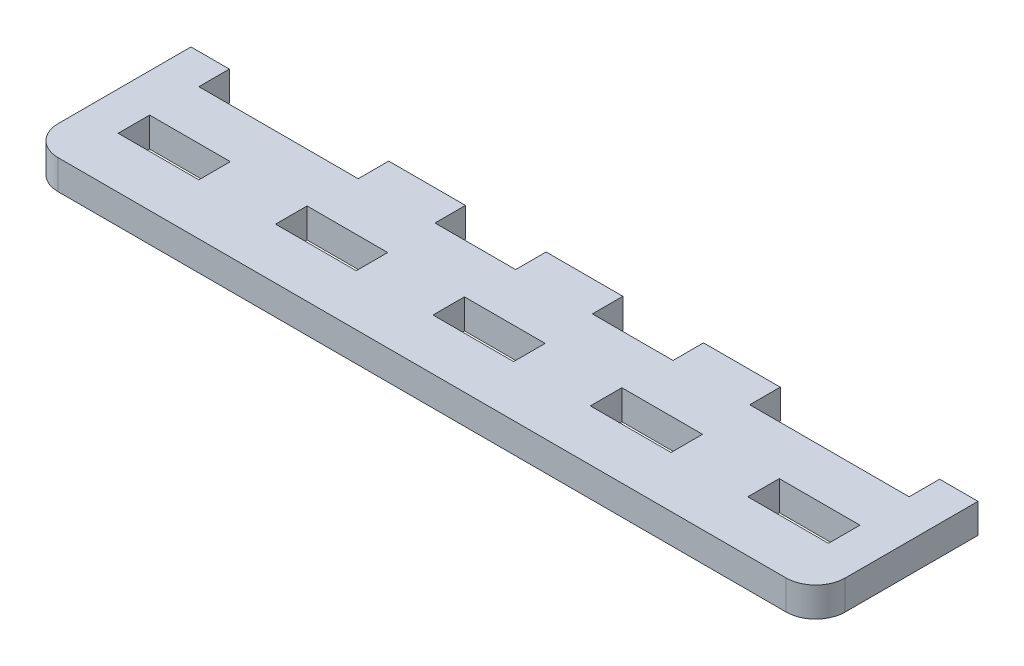
SolidWorks part; units mm, degrees
ref_plane "Front Plane" through (0, 0, 0) normal (0, 0, 1) x (1, 0, 0)
ref_plane "Top Plane" through (0, 0, 0) normal (0, 1, 0) x (1, 0, 0)
ref_plane "Right Plane" through (0, 0, 0) normal (1, 0, 0) x (0, 0, -1)
sketch "Sketch1" plane through (0, 0, 0) normal (0, 1, 0) x (1, 0, 0)
  line L0 (80, -80) -> (80, 0) construction
  line L1 (0, 0) -> (80, 0)
  line L2 (0, 0) -> (0, -16.5)
  line L3 (0, -16.5) -> (80, -16.5)
  line L4 (80, 0) -> (80, -16.5)
sketch "Sketch2" plane through (0, 0, 0) normal (1, 0, 0) x (0, 0, -1)
  line L1 (0, 0) -> (-16.5, 0)
  line L2 (0, 0) -> (0, -3)
  line L3 (0, -3) -> (-16.5, -3)
  line L4 (-16.5, 0) -> (-16.5, -3)
extrude "Boss-Extrude1" add sketch "Sketch1" against normal up to vertex (3 mm away) up to point (0, -3, 0)
sketch "Sketch3" plane through (0, 0, 0) normal (0, 1, 0) x (1, 0, 0)
  line L4 (12, -11.2) -> (12, -8.2)
  line L5 (12, -8.2) -> (4, -8.2)
  line L6 (4, -8.2) -> (4, -11.2)
  line L7 (4, -11.2) -> (12, -11.2)
  line L8 (12, -11.2) -> (12, -8.2) construction
  line L9 (12, -8.2) -> (4, -8.2) construction
  line L10 (4, -8.2) -> (4, -11.2) construction
  line L11 (4, -11.2) -> (12, -11.2) construction
  line L12 (28, 0) -> (28, -3)
  line L13 (36, 0) -> (28, 0)
  line L14 (36, -3) -> (36, 0)
  line L15 (28, -3) -> (36, -3)
  line L16 (28, 0) -> (28, -3) construction
  line L17 (36, 0) -> (28, 0) construction
  line L18 (36, -3) -> (36, 0) construction
  line L19 (28, -3) -> (36, -3) construction
  line L20 (36, -8.2) -> (36, -11.2)
  line L21 (44, -8.2) -> (36, -8.2)
  line L22 (44, -11.2) -> (44, -8.2)
  line L23 (36, -11.2) -> (44, -11.2)
  line L24 (36, -8.2) -> (36, -11.2) construction
  line L25 (44, -8.2) -> (36, -8.2) construction
  line L26 (44, -11.2) -> (44, -8.2) construction
  line L27 (36, -11.2) -> (44, -11.2) construction
  line L28 (20, -8.2) -> (20, -11.2)
  line L29 (28, -8.2) -> (20, -8.2)
  line L30 (28, -11.2) -> (28, -8.2)
  line L31 (20, -11.2) -> (28, -11.2)
  line L32 (20, -8.2) -> (20, -11.2) construction
  line L33 (28, -8.2) -> (20, -8.2) construction
  line L34 (28, -11.2) -> (28, -8.2) construction
  line L35 (20, -11.2) -> (28, -11.2) construction
  line L36 (20, -3) -> (20, 0)
  line L37 (20, 0) -> (4, 0)
  line L38 (4, 0) -> (4, -3)
  line L39 (4, -3) -> (20, -3)
  line L40 (20, -3) -> (20, 0) construction
  line L41 (20, 0) -> (4, 0) construction
  line L42 (4, 0) -> (4, -3) construction
  line L43 (4, -3) -> (20, -3) construction
  line L44 (44, 0) -> (44, -3)
  line L45 (52, 0) -> (44, 0)
  line L46 (52, -3) -> (52, 0)
  line L47 (44, -3) -> (52, -3)
  line L48 (44, 0) -> (44, -3) construction
  line L49 (52, 0) -> (44, 0) construction
  line L50 (52, -3) -> (52, 0) construction
  line L51 (44, -3) -> (52, -3) construction
  line L52 (60, -11.2) -> (60, -8.2)
  line L53 (60, -8.2) -> (52, -8.2)
  line L54 (52, -8.2) -> (52, -11.2)
  line L55 (52, -11.2) -> (60, -11.2)
  line L56 (60, -11.2) -> (60, -8.2) construction
  line L57 (60, -8.2) -> (52, -8.2) construction
  line L58 (52, -8.2) -> (52, -11.2) construction
  line L59 (52, -11.2) -> (60, -11.2) construction
  line L60 (68, -8.2) -> (68, -11.2)
  line L61 (76, -8.2) -> (68, -8.2)
  line L62 (76, -11.2) -> (76, -8.2)
  line L63 (68, -11.2) -> (76, -11.2)
  line L64 (68, -8.2) -> (68, -11.2) construction
  line L65 (76, -8.2) -> (68, -8.2) construction
  line L66 (76, -11.2) -> (76, -8.2) construction
  line L67 (68, -11.2) -> (76, -11.2) construction
  line L68 (76, 0) -> (60, 0)
  line L69 (60, 0) -> (60, -3)
  line L70 (60, -3) -> (76, -3)
  line L71 (76, -3) -> (76, 0)
  line L72 (76, 0) -> (60, 0) construction
  line L73 (60, 0) -> (60, -3) construction
  line L74 (60, -3) -> (76, -3) construction
  line L75 (76, -3) -> (76, 0) construction
  line L108 (12.1, -11.3) -> (12.1, -8.1)
  line L109 (12.1, -8.1) -> (3.9, -8.1)
  line L110 (3.9, -8.1) -> (3.9, -11.3)
  line L111 (3.9, -11.3) -> (12.1, -11.3)
  line L112 (27.9, 0.1) -> (27.9, -3.1)
  line L113 (27.9, -3.1) -> (36.1, -3.1)
  line L114 (36.1, -3.1) -> (36.1, 0.1)
  line L115 (36.1, 0.1) -> (27.9, 0.1)
  line L116 (35.9, -8.1) -> (35.9, -11.3)
  line L117 (35.9, -11.3) -> (44.1, -11.3)
  line L118 (44.1, -11.3) -> (44.1, -8.1)
  line L119 (44.1, -8.1) -> (35.9, -8.1)
  line L120 (19.9, -8.1) -> (19.9, -11.3)
  line L121 (19.9, -11.3) -> (28.1, -11.3)
  line L122 (28.1, -11.3) -> (28.1, -8.1)
  line L123 (28.1, -8.1) -> (19.9, -8.1)
  line L124 (20.1, -3.1) -> (20.1, 0.1)
  line L125 (20.1, 0.1) -> (3.9, 0.1)
  line L126 (3.9, 0.1) -> (3.9, -3.1)
  line L127 (3.9, -3.1) -> (20.1, -3.1)
  line L128 (43.9, 0.1) -> (43.9, -3.1)
  line L129 (43.9, -3.1) -> (52.1, -3.1)
  line L130 (52.1, -3.1) -> (52.1, 0.1)
  line L131 (52.1, 0.1) -> (43.9, 0.1)
  line L132 (60.1, -11.3) -> (60.1, -8.1)
  line L133 (60.1, -8.1) -> (51.9, -8.1)
  line L134 (51.9, -8.1) -> (51.9, -11.3)
  line L135 (51.9, -11.3) -> (60.1, -11.3)
  line L136 (67.9, -8.1) -> (67.9, -11.3)
  line L137 (67.9, -11.3) -> (76.1, -11.3)
  line L138 (76.1, -11.3) -> (76.1, -8.1)
  line L139 (76.1, -8.1) -> (67.9, -8.1)
  line L140 (76.1, 0.1) -> (59.9, 0.1)
  line L141 (59.9, 0.1) -> (59.9, -3.1)
  line L142 (59.9, -3.1) -> (76.1, -3.1)
  line L143 (76.1, -3.1) -> (76.1, 0.1)
  dimension "D1" = 0
  dimension "D2" = 0
  dimension "D3" = 0
  dimension "D4" = 0
  dimension "D5" = 0
  dimension "D6" = 0
  dimension "D7" = 0
  dimension "D8" = 0
  dimension "D9" = 0
  dimension "D10" = 0.1
extrude "Cut-Extrude1" cut sketch "Sketch3" against normal through all
fillet "Fillet1" radius 3 2 edges at (80, -1.5, 16.5) (0, -1.5, 16.5)
